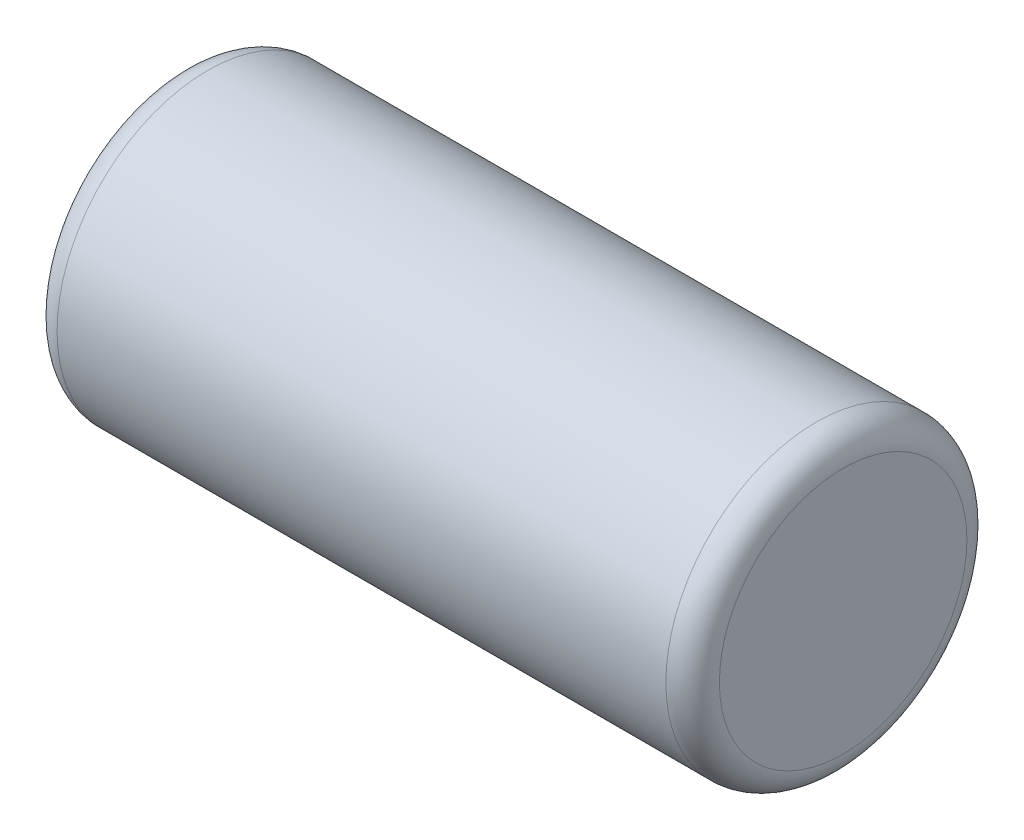
SolidWorks part; units mm, degrees
ref_plane "Front Plane" through (0, 0, 0) normal (0, 0, 1) x (1, 0, 0)
ref_plane "Top Plane" through (0, 0, 0) normal (0, 1, 0) x (1, 0, 0)
ref_plane "Right Plane" through (0, 0, 0) normal (1, 0, 0) x (0, 0, -1)
ref_plane "Plane1" through (0, 0, 0) normal (0, 0, 1) x (1, 0, 0)
sketch "Sketch1" plane through (0, 0, 0) normal (0, 0, 1) x (1, 0, 0)
  line L0 (1.35, 3.75) -> (1.35, 4.3667)
  line L1 (1.4833, 4.5) -> (4.5167, 4.5)
  line L2 (4.65, 4.3667) -> (4.65, 3.75)
  line L3 (4.65, 3.75) -> (1.35, 3.75)
  line L4 (50, 3.75) -> (-50, 3.75) construction
  arc A0 (1.35, 4.3667) -> (1.4833, 4.5) centre (1.4833, 4.3667) cw
  arc A1 (4.5167, 4.5) -> (4.65, 4.3667) centre (4.5167, 4.3667) cw
revolve "Revolve1" add sketch "Sketch1" angle 360 about L4
